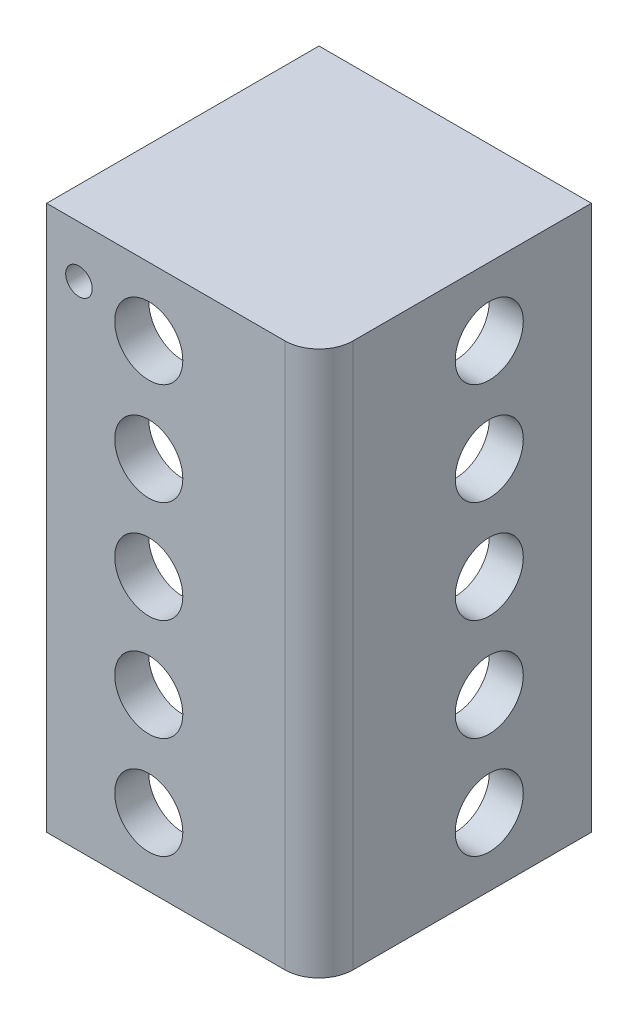
SolidWorks part; units mm, degrees
material "PET"
ref_plane "Front Plane" through (0, 0, 0) normal (0, 0, 1) x (1, 0, 0)
ref_plane "Top Plane" through (0, 0, 0) normal (0, 1, 0) x (1, 0, 0)
ref_plane "Right Plane" through (0, 0, 0) normal (1, 0, 0) x (0, 0, -1)
sketch "Sketch2" plane through (0, 0, 0) normal (0, 1, 0) x (1, 0, 0)
  line L1 (-41.3514, 76.4779) -> (60.2486, 76.4779)
  line L2 (-41.3514, 76.4779) -> (-41.3514, -25.1221)
  line L3 (-41.3514, -25.1221) -> (60.2486, -25.1221)
  line L4 (60.2486, 76.4779) -> (60.2486, -25.1221)
  dimension "D1" = 101.6
  dimension "D2" = 101.6
extrude "Boss-Extrude1" add sketch "Sketch2" along normal blind 203.2
ref_plane "Plane1" through (0, 101.6, 0) normal (0, 1, 0) x (1, 0, 0)
sketch "Sketch4" plane through (0, 101.6, 0) normal (0, 1, 0) x (1, 0, 0)
  line L0 (60.2486, -25.1221) -> (60.2486, 76.4779) construction
  line L1 (-41.3514, 76.4779) -> (47.5486, 76.4779)
  line L2 (-41.3514, 76.4779) -> (-41.3514, -12.4221)
  line L3 (-41.3514, -12.4221) -> (47.5486, -12.4221)
  line L4 (47.5486, 76.4779) -> (47.5486, -12.4221)
  line L5 (-41.3514, -25.1221) -> (60.2486, -25.1221) construction
  dimension "D1" = 12.7
  dimension "D2" = 12.7
extrude "Cut-Extrude1" cut sketch "Sketch4" along normal mid plane 190.5
fillet "Fillet1" radius 12.7 2 edges at (60.2486, 101.6, 25.1221) (47.5486, 101.6, 12.4221)
sketch "Sketch5" plane through (0, 0, 25.1221) normal (0, 0, 1) x (1, 0, 0)
  line L0 (-41.3514, 203.2) -> (47.5486, 203.2) construction
  line L1 (-41.3514, 0) -> (47.5486, 0) construction
  line L2 (-41.3514, 203.2) -> (-41.3514, 0) construction
  circle A0 centre (-3.2514, 177.8) radius 12.7
  circle A1 centre (-3.2514, 139.7) radius 12.7
  circle A2 centre (-3.2514, 101.6) radius 12.7
  circle A3 centre (-3.2514, 63.5) radius 12.7
  circle A4 centre (-3.2514, 25.4) radius 12.7
  dimension "D1" = 25.4
  dimension "D3" = 25.4
  dimension "D4" = 38.1
  dimension "D2" = 5
extrude "Cut-Extrude2" cut sketch "Sketch5" against normal through all
sketch "Sketch6" plane through (60.2486, 0, 0) normal (1, 0, 0) x (0, 0, -1)
  line L0 (-12.4221, 203.2) -> (76.4779, 203.2) construction
  line L1 (76.4779, 203.2) -> (76.4779, 0) construction
  circle A0 centre (38.3779, 177.8) radius 12.7
  circle A1 centre (38.3779, 139.7) radius 12.7
  circle A2 centre (38.3779, 101.6) radius 12.7
  circle A3 centre (38.3779, 63.5) radius 12.7
  circle A4 centre (38.3779, 25.4) radius 12.7
  dimension "D1" = 25.4
  dimension "D2" = 38.1
  dimension "D3" = 5
extrude "Cut-Extrude3" cut sketch "Sketch6" against normal through all
sketch "Sketch7" plane through (0, 6.35, 0) normal (0, 1, 0) x (1, 0, 0)
  line L0 (60.2486, -12.4221) -> (60.2486, 76.4779) construction
  line L1 (-41.3514, 76.4779) -> (47.5486, 76.4779)
  line L2 (-41.3514, 76.4779) -> (-41.3514, -12.4221)
  line L3 (-41.3514, -12.4221) -> (34.8486, -12.4221)
  line L4 (47.5486, 76.4779) -> (47.5486, 0.2779)
  line L5 (-41.3514, -25.1221) -> (47.5486, -25.1221) construction
  arc A0 (34.8486, -12.4221) -> (47.5486, 0.2779) centre (34.8486, 0.2779) ccw
  dimension "D3" = 12.7
  dimension "D1" = 12.7
  dimension "D2" = 12.7
extrude "Cut-Extrude4" cut sketch "Sketch7" against normal through all
sketch "Sketch31" plane through (0, 196.85, 0) normal (0, -1, 0) x (1, 0, 0)
  line L24 (-41.3514, -76.4779) -> (-41.3514, 12.4221) construction
  line L25 (-41.3514, 2.2621) -> (-18.4914, 2.2621)
  line L26 (-41.3514, 2.2621) -> (-41.3514, -6.6279)
  line L27 (-41.3514, -6.6279) -> (-18.4914, -6.6279)
  line L28 (-18.4914, 2.2621) -> (-18.4914, -6.6279)
  line L29 (-41.3514, 12.4221) -> (34.8486, 12.4221) construction
  line L30 (-41.3514, -18.5659) -> (-18.4914, -18.5659)
  line L31 (-41.3514, -18.5659) -> (-41.3514, -27.4559)
  line L32 (-41.3514, -27.4559) -> (-18.4914, -27.4559)
  line L33 (-18.4914, -18.5659) -> (-18.4914, -27.4559)
  dimension "D1" = 8.89
  dimension "D2" = 11.938
  dimension "D3" = 22.86
  dimension "D4" = 10.16
extrude "Boss-Extrude2" add sketch "Sketch31" along normal blind 25.4
fillet "Fillet5" radius 12.7 2 edges at (-41.3514, 171.45, -2.1829) (-41.3514, 171.45, -23.0109)
fillet "Fillet6" radius 6.35 2 edges at (-18.4914, 171.45, -2.1829) (-18.4914, 171.45, -23.0109)
sketch "Sketch38" plane through (0, 0, -27.4559) normal (0, 0, -1) x (-1, 0, 0)
  line L0 (18.4914, 177.8) -> (18.4914, 196.85) construction
  line L1 (28.6514, 171.45) -> (24.8414, 171.45) construction
  circle A0 centre (29.2864, 184.023) radius 4.953
  dimension "D1" = 9.906
  dimension "D2" = 10.795
  dimension "D3" = 12.573
extrude "Cut-Extrude7" cut sketch "Sketch38" against normal through all and the other way through all
